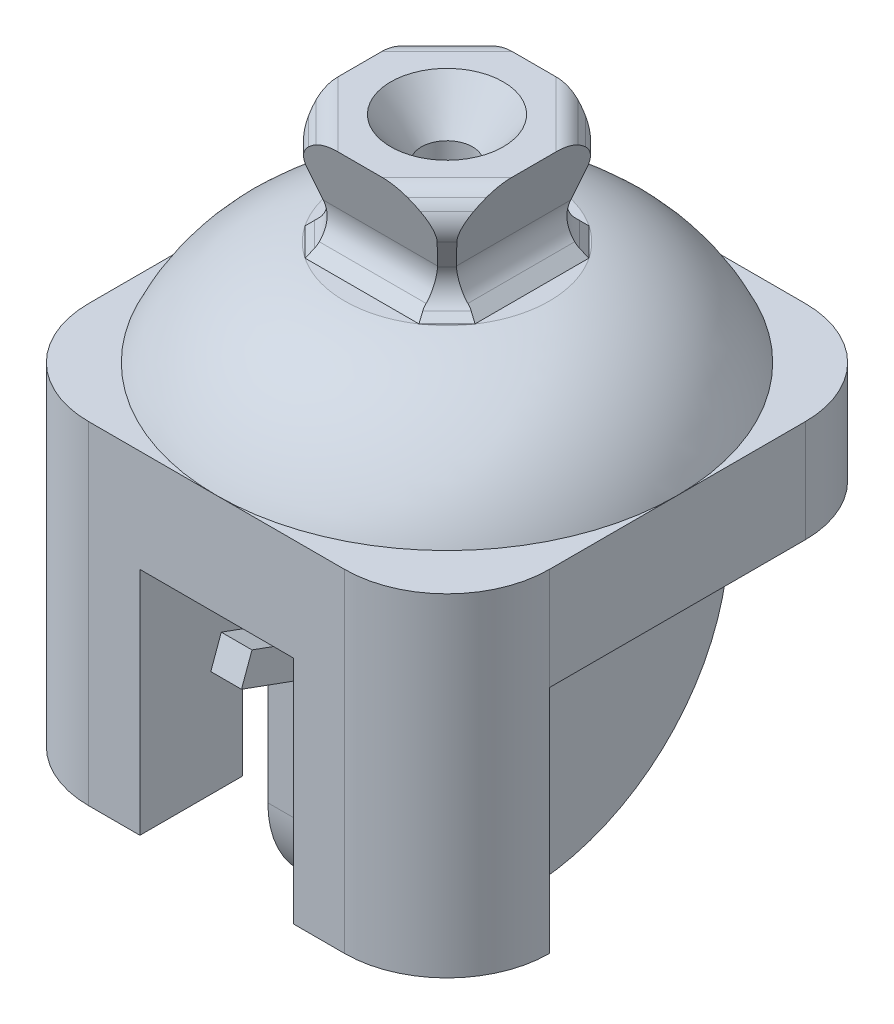
SolidWorks part; units mm, degrees
material "6061-T6 (SS)"
ref_plane "Front Plane" through (0, 0, 0) normal (0, 0, 1) x (1, 0, 0)
ref_plane "Top Plane" through (0, 0, 0) normal (0, 1, 0) x (1, 0, 0)
ref_plane "Right Plane" through (0, 0, 0) normal (1, 0, 0) x (0, 0, -1)
sketch "Sketch4" plane through (0, 0, 0) normal (0, 0, 1) x (1, 0, 0)
  line L1 (-8.5, -5.5) -> (8.5, -5.5)
  line L2 (-8.5, -5.5) -> (-8.5, 5.5)
  line L3 (-8.5, 5.5) -> (8.5, 5.5)
  line L4 (8.5, -5.5) -> (8.5, 5.5)
  line L5 (-8.5, -5.5) -> (8.5, 5.5) construction
  line L6 (-8.5, 5.5) -> (8.5, -5.5) construction
  point P0 (0, 0)
  dimension "D1" = 11
  dimension "D2" = 17
extrude "Boss-Extrude2" add sketch "Sketch4" along normal mid plane 17
sketch "Sketch5" plane through (0, 0, 0) normal (1, 0, 0) x (0, 0, -1)
  line L0 (0, -10) -> (0, 10) construction
  line L1 (8.5, 5.5) -> (6.5025, -1.2915)
  line L2 (8.5, -5.5) -> (7.2593, -4.2593)
  line L3 (-8.5, -5.5) -> (-7.2593, -4.2593)
  line L4 (-8.5, 5.5) -> (-6.5025, -1.2915)
  line L5 (-8.5, 5.5) -> (-8.5, -5.5)
  line L6 (8.5, -5.5) -> (8.5, 5.5)
  arc A0 (7.2593, -4.2593) -> (6.5025, -1.2915) centre (9.3806, -2.138) cw
  arc A1 (-7.2593, -4.2593) -> (-6.5025, -1.2915) centre (-9.3806, -2.138) ccw
  point P12 (6, -3)
  point P16 (-6, -3)
  dimension "D5" = 3
  dimension "D1" = 10
  dimension "D2" = 20
  dimension "D3" = 6
  dimension "D4" = 45
extrude "Cut-Extrude1" cut sketch "Sketch5" against normal mid plane 27
sketch "Sketch7" plane through (0, 0, 0) normal (0, 0, 1) x (1, 0, 0)
  line L0 (0, -10) -> (0, 10) construction
  line L1 (8.5, 5.5) -> (6.5025, -1.2915)
  line L2 (8.5, -5.5) -> (7.2593, -4.2593)
  line L3 (-8.5, -5.5) -> (-7.2593, -4.2593)
  line L4 (-8.5, 5.5) -> (-6.5025, -1.2915)
  line L5 (-8.5, 5.5) -> (-8.5, -5.5)
  line L6 (8.5, -5.5) -> (8.5, 5.5)
  line L7 (8.5, -4.2593) -> (8.5, -5.5) construction
  arc A0 (7.2593, -4.2593) -> (6.5025, -1.2915) centre (9.3806, -2.138) cw
  arc A1 (-7.2593, -4.2593) -> (-6.5025, -1.2915) centre (-9.3806, -2.138) ccw
  point P12 (-6, -3)
  dimension "D3" = 3
  dimension "D1" = 20
  dimension "D2" = 45
  dimension "D4" = 16.389
extrude "Cut-Extrude2" cut sketch "Sketch7" against normal mid plane 27
sketch "Sketch8" plane through (0, 5.5, 0) normal (0, 1, 0) x (1, 0, 0)
  line L0 (3.5355, 3.5355) -> (-3.5355, -3.5355) construction
  line L1 (-5, 0) -> (5, 0) construction
  line L2 (-3.5355, 3.5355) -> (3.5355, -3.5355) construction
  line L3 (0, 5) -> (0, -5) construction
  dimension "D1" = 10
  dimension "D2" = 10
  dimension "D3" = 10
  dimension "D4" = 45
  dimension "D5" = 45
  dimension "D6" = 10
sketch "Sketch9" plane through (0, 0, 0) normal (0, 1, 0) x (1, 0, 0)
  line L0 (3.5355, 3.5355) -> (-3.5355, -3.5355) construction
  line L1 (-5, 0) -> (5, 0) construction
  line L2 (-3.5355, 3.5355) -> (3.5355, -3.5355) construction
  line L3 (0, 5) -> (0, -5) construction
  point P8 (0, 0)
  point P10 (0, 0)
  point P11 (0, 0)
  dimension "D1" = 10
  dimension "D2" = 10
  dimension "D3" = 10
  dimension "D4" = 45
  dimension "D5" = 45
  dimension "D6" = 10
ref_plane "Plane1" through (0, 0, 0) normal (0.7071, 0, 0.7071) x (0.7071, 0, -0.7071)
ref_plane "Plane2" through (0, 0, 0) normal (0.7071, 0, -0.7071) x (-0.7071, 0, -0.7071)
sketch "Sketch11" plane through (0, 0, 0) normal (0.7071, 0, 0.7071) x (0.7071, 0, -0.7071)
  line L0 (-10, 5.5) -> (10, 5.5) construction
  line L1 (0, -5.5) -> (0, 5.5) construction
  line L2 (10, 5.5) -> (10, -5.5) construction
  line L3 (0, -5.5) -> (12.0208, -5.5) construction
  line L4 (10, -5.5) -> (0, -5.5) construction
  line L5 (10, -5.5) -> (9.1595, -4.6595)
  line L6 (10, 5.5) -> (10, 2.3) construction
  line L7 (0, 5.5) -> (8.25, 5.5) construction
  line L8 (9.6935, 1.5413) -> (8.4993, -1.4144)
  line L10 (10, -5.5) -> (14, -5.5)
  line L11 (14, -5.5) -> (14, 5.5)
  line L12 (14, 5.5) -> (8.25, 5.5)
  line L13 (-14, 5.5) -> (-8.25, 5.5)
  line L14 (-9.6935, 1.5413) -> (-8.4993, -1.4144)
  line L15 (-10, -5.5) -> (-9.1595, -4.6595)
  line L16 (-10, -5.5) -> (-14, -5.5)
  line L17 (-14, -5.5) -> (-14, 5.5)
  arc A0 (9.5819, 4.0331) -> (8.25, 5.5) centre (6.1993, 2.3) ccw
  arc A1 (9.5819, 4.0331) -> (9.6935, 1.5413) centre (6.9119, 2.6651) cw
  arc A2 (9.1595, -4.6595) -> (8.4993, -1.4144) centre (11.2808, -2.5382) cw
  arc A3 (-9.5819, 4.0331) -> (-9.6935, 1.5413) centre (-6.9119, 2.6651) ccw
  arc A4 (-9.5819, 4.0331) -> (-8.25, 5.5) centre (-6.1993, 2.3) cw
  arc A5 (-9.1595, -4.6595) -> (-8.4993, -1.4144) centre (-11.2808, -2.5382) ccw
  dimension "D7" = 3
  dimension "D8" = 3
  dimension "D1" = 20
  dimension "D2" = 11
  dimension "D3" = 45
  dimension "D4" = 8.25
  dimension "D5" = 3.2
  dimension "D6" = 22
  dimension "D9" = 4
extrude "Cut-Extrude3" cut sketch "Sketch11" against normal mid plane 27
sketch "Sketch12" plane through (0, 0, 0) normal (0.7071, 0, -0.7071) x (-0.7071, 0, -0.7071)
  line L0 (-10, 5.5) -> (10, 5.5) construction
  line L1 (0, -5.5) -> (0, 5.5) construction
  line L2 (10, 5.5) -> (10, -5.5) construction
  line L3 (10, -5.5) -> (0, -5.5) construction
  line L4 (10, -5.5) -> (9.1595, -4.6595)
  line L5 (10, 5.5) -> (10, 2.3) construction
  line L6 (0, 5.5) -> (8.25, 5.5) construction
  line L7 (9.6935, 1.5413) -> (8.4993, -1.4144)
  line L8 (10, -5.5) -> (14, -5.5)
  line L9 (14, -5.5) -> (14, 5.5)
  line L10 (14, 5.5) -> (8.25, 5.5)
  line L11 (-14, 5.5) -> (-8.25, 5.5)
  line L12 (-9.6935, 1.5413) -> (-8.4993, -1.4144)
  line L13 (-10, -5.5) -> (-9.1595, -4.6595)
  line L14 (-10, -5.5) -> (-14, -5.5)
  line L15 (-14, -5.5) -> (-14, 5.5)
  arc A0 (9.5819, 4.0331) -> (8.25, 5.5) centre (6.1993, 2.3) ccw
  arc A1 (9.5819, 4.0331) -> (9.6935, 1.5413) centre (6.9119, 2.6651) cw
  arc A2 (9.1595, -4.6595) -> (8.4993, -1.4144) centre (11.2808, -2.5382) cw
  arc A3 (-9.5819, 4.0331) -> (-9.6935, 1.5413) centre (-6.9119, 2.6651) ccw
  arc A4 (-9.5819, 4.0331) -> (-8.25, 5.5) centre (-6.1993, 2.3) cw
  arc A5 (-9.1595, -4.6595) -> (-8.4993, -1.4144) centre (-11.2808, -2.5382) ccw
  dimension "D7" = 3
  dimension "D8" = 3
  dimension "D1" = 20
  dimension "D2" = 11
  dimension "D3" = 45
  dimension "D4" = 8.25
  dimension "D5" = 3.2
  dimension "D6" = 22
  dimension "D9" = 4
extrude "Cut-Extrude4" cut sketch "Sketch12" against normal mid plane 27
sketch "Sketch14" plane through (0, 0, 0) normal (0, 0, 1) x (1, 0, 0)
  line L0 (0, 5.5) -> (0, -5.5) construction
  line L1 (0, 5.5) -> (5.5, 5.5)
  line L2 (3.1673, 5.5) -> (8.5, 5.5) construction
  line L3 (5.5, 5.5) -> (5.5, 1.5) construction
  line L4 (0, 1.5) -> (2.5, 1.5) construction
  line L5 (2.5, 1.5) -> (5.5, 5.5)
  line L6 (2.5, 1.5) -> (2.5, -5.5)
  line L7 (-5.6421, -5.5) -> (5.6421, -5.5) construction
  line L8 (0, -5.5) -> (0, 5.5)
  line L9 (2.5, -5.5) -> (0, -5.5)
  dimension "D1" = 11
  dimension "D2" = 5.5
  dimension "D3" = 4
  dimension "D4" = 2.5
revolve "Cut-Revolve1" cut sketch "Sketch14" angle 360 about L8
fillet "Fillet1" radius 2 4 edges at (5.8336, 5.5, -5.8336) (-5.8336, 5.5, -5.8336) (-5.8336, 5.5, 5.8336) (5.8336, 5.5, 5.8336)
sketch "Sketch15" plane through (0, 0, 0) normal (1, 0, 0) x (0, 0, -1)
  line L0 (0, -5.5) -> (0, -15.5) construction
  line L1 (-5.6421, -5.5) -> (5.6421, -5.5) construction
  line L3 (0, -15.5) -> (22.5, -15.5)
  line L4 (0, -15.5) -> (0, -5.5)
  line L5 (0, -5.5) -> (0, -5.3)
  line L6 (0, -5.3) -> (9.998, -5.3)
  arc A0 (9.998, -5.3) -> (22.5, -15.5) centre (6.077, -22.8677) cw
  dimension "D4" = 18
  dimension "D1" = 10
  dimension "D2" = 10
  dimension "D3" = 22.5
  dimension "D5" = 0.2
revolve "Revolve1" add sketch "Sketch15" angle 360 about L0
sketch "Sketch16" plane through (0, -15.5, 0) normal (0, -1, 0) x (1, 0, 0)
  line L1 (-22.5, -22.5) -> (22.5, -22.5)
  line L2 (-22.5, -22.5) -> (-22.5, 22.5)
  line L3 (-22.5, 22.5) -> (22.5, 22.5)
  line L4 (22.5, -22.5) -> (22.5, 22.5)
  line L5 (-22.5, -22.5) -> (22.5, 22.5) construction
  line L6 (-22.5, 22.5) -> (22.5, -22.5) construction
  point P0 (0, 0)
  dimension "D1" = 45
  dimension "D2" = 45
extrude "Boss-Extrude3" add sketch "Sketch16" along normal blind 10
sketch "Sketch17" plane through (0, -25.5, 0) normal (0, -1, 0) x (1, 0, 0)
  line L0 (-5, 12.5) -> (-5, -22.5)
  line L1 (22.5, 22.5) -> (-22.5, 22.5) construction
  line L2 (-22.5, -22.5) -> (22.5, -22.5) construction
  line L3 (5, 12.5) -> (5, -22.5)
  line L4 (-5, 12.5) -> (5, 12.5)
  line L5 (-22.5, 22.5) -> (-22.5, -22.5) construction
  line L6 (22.5, -22.5) -> (22.5, 22.5) construction
  line L7 (5, -22.5) -> (-5, -22.5)
  dimension "D1" = 17.5
  dimension "D2" = 17.5
  dimension "D3" = 10
extrude "Boss-Extrude4" add sketch "Sketch17" along normal blind 33.5
sketch "Sketch18" plane through (0, -25.5, 0) normal (0, -1, 0) x (1, 0, 0)
  line L1 (22.5, 22.5) -> (7.5, 22.5)
  line L2 (22.5, 22.5) -> (22.5, 12.5)
  line L3 (22.5, 12.5) -> (7.5, 12.5)
  line L4 (7.5, 22.5) -> (7.5, 12.5)
  line L5 (-22.5, 22.5) -> (-7.5, 22.5)
  line L6 (-22.5, 22.5) -> (-22.5, 12.5)
  line L7 (-22.5, 12.5) -> (-7.5, 12.5)
  line L8 (-7.5, 22.5) -> (-7.5, 12.5)
  dimension "D1" = 15
  dimension "D2" = 15
  dimension "D3" = 10
  dimension "D4" = 10
extrude "Boss-Extrude5" add sketch "Sketch18" along normal blind 22.5
sketch "Sketch19" plane through (5, 0, 0) normal (1, 0, 0) x (0, 0, -1)
  line L0 (22.5, -25.5) -> (-12.5, -25.5) construction
  line L1 (-22.5, -48) -> (-22.5, -15.5) construction
  circle A0 centre (-3.5, -48) radius 6
  dimension "D3" = 12
  dimension "D1" = 22.5
  dimension "D2" = 19
extrude "Cut-Extrude5" cut sketch "Sketch19" against normal through all
fillet "Fillet3" radius 10 5 edges at (-22.5, -31.75, 22.5) (22.5, -31.75, 22.5) (-22.5, -20.5, -22.5) (22.5, -20.5, -22.5) (0, -59, 12.5)
fillet "Fillet4" radius 20 1 edges at (0, -59, -22.5)
sketch "Sketch20" plane through (0, 0, 12.5) normal (0, 0, 1) x (1, 0, 0)
  line L0 (1.5, -25.5) -> (1.5, -34)
  line L1 (5, -25.5) -> (-5, -25.5) construction
  line L2 (1.5, -34) -> (-1.5, -34)
  line L3 (-1.5, -34) -> (-1.5, -25.5)
  line L5 (-7.5, -48) -> (-7.5, -25.5) construction
  line L6 (1.5, -25.5) -> (-1.5, -25.5)
  dimension "D1" = 8.5
  dimension "D2" = 3
  dimension "D3" = 6
extrude "Boss-Extrude6" add sketch "Sketch20" along normal blind 2.5
sketch "Sketch21" plane through (1.5, 0, 0) normal (1, 0, 0) x (0, 0, -1)
  line L3 (-15, -30.8075) -> (-15, -34)
  line L5 (-15, -34) -> (-21.5778, -31.6059)
  line L6 (-21.5778, -31.6059) -> (-20.5518, -28.7868)
  line L8 (-15, -34) -> (-15, -25.5) construction
  line L10 (-20.5518, -28.7868) -> (-15, -30.8075)
  dimension "D1" = 90
  dimension "D2" = 3
  dimension "D3" = 7
  dimension "D4" = 90
  dimension "D5" = 70
extrude "Boss-Extrude7" add sketch "Sketch21" against normal blind 3
